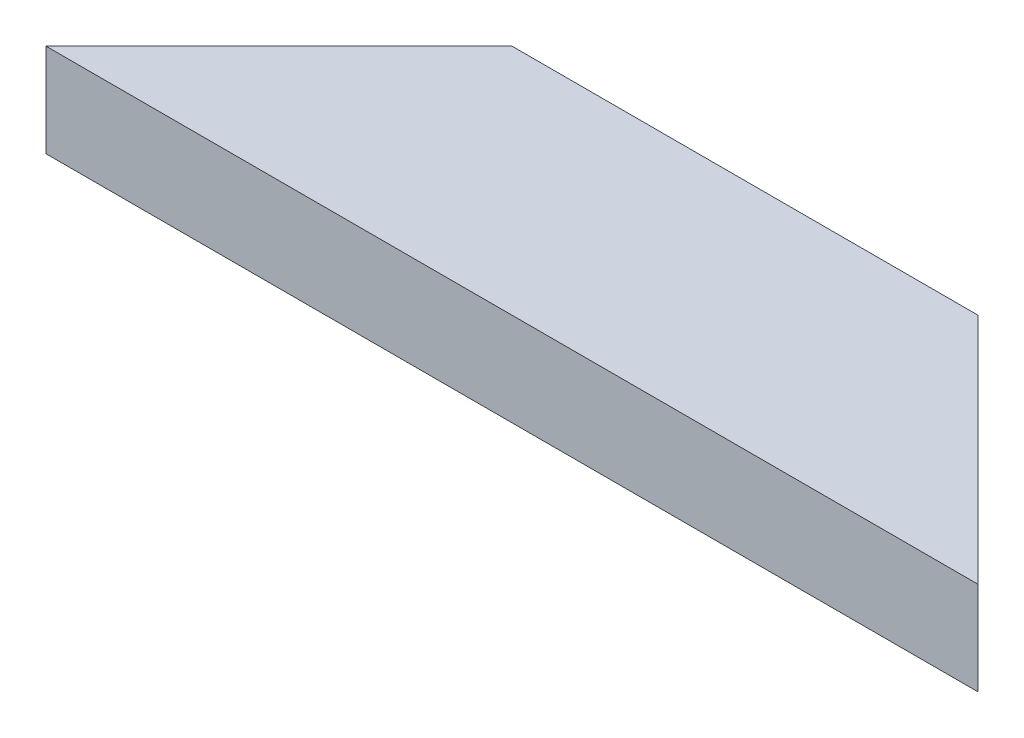
SolidWorks part; units mm, degrees
material "ASTM A36 Acier"
ref_plane "Front Plane" through (0, 0, 0) normal (0, 0, 1) x (1, 0, 0)
ref_plane "Top Plane" through (0, 0, 0) normal (0, 1, 0) x (1, 0, 0)
ref_plane "Right Plane" through (0, 0, 0) normal (1, 0, 0) x (0, 0, -1)
sketch "Sketch1" plane through (0, 0, 0) normal (0, 1, 0) x (1, 0, 0)
  line L0 (25, 0) -> (-25, 0)
  line L1 (-25, 0) -> (-50, -25)
  line L2 (-50, -25) -> (50, -25)
  line L3 (50, -25) -> (25, 0)
  point P4 (0, 0)
  dimension "D1" = 45
  dimension "D2" = 45
  dimension "D3" = 25
  dimension "D4" = 50
extrude "Boss-Extrude1" add sketch "Sketch1" along normal mid plane 10
